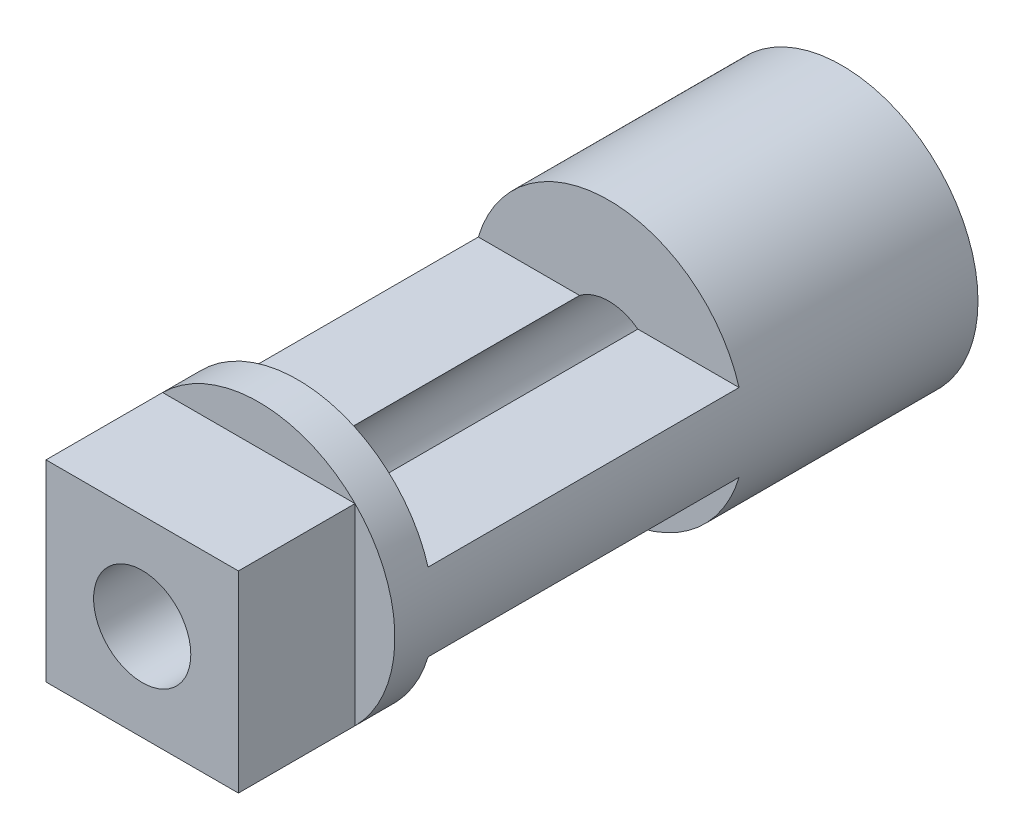
SolidWorks part; units mm, degrees
ref_plane "Front Plane" through (0, 0, 0) normal (0, 0, 1) x (1, 0, 0)
ref_plane "Top Plane" through (0, 0, 0) normal (0, 1, 0) x (1, 0, 0)
ref_plane "Right Plane" through (0, 0, 0) normal (1, 0, 0) x (0, 0, -1)
sketch "Sketch3" plane through (0, 0, 0) normal (0, 0, 1) x (1, 0, 0)
  circle A0 centre (0, 0) radius 1.25 construction
  circle A1 centre (0, 0) radius 1.25
  circle A2 centre (0, 0) radius 3.5 construction
  circle A3 centre (0, 0) radius 3.5
extrude "Boss-Extrude1" add sketch "Sketch3" along normal up to vertex (23 mm away) from vertex at 5
sketch "Sketch4" plane through (0, 0, 0) normal (1, 0, 0) x (0, 0, -1)
  line L0 (-23, 0) -> (-26, 0) construction
  line L1 (-19, 3.5) -> (-11, 3.5)
  line L2 (-19, 3.5) -> (-19, 1)
  line L3 (-19, 1) -> (-11, 1)
  line L4 (-11, 3.5) -> (-11, 1)
  line L5 (-5, 3.5) -> (-23, 3.5) construction
  dimension "D1" = 1
extrude "Cut-Extrude1" cut sketch "Sketch4" against normal through all both and the other way through all
mirror "Mirror1" about plane through (0, 0, 0) normal (0, 1, 0) of "Cut-Extrude1"
sketch "Sketch5" plane through (0, 0, 23) normal (0, 0, 1) x (1, 0, 0)
  line L1 (-2.4749, -2.4749) -> (2.4749, -2.4749)
  line L2 (-2.4749, -2.4749) -> (-2.4749, 2.4749)
  line L3 (-2.4749, 2.4749) -> (2.4749, 2.4749)
  line L4 (2.4749, -2.4749) -> (2.4749, 2.4749)
  line L5 (-2.4749, -2.4749) -> (2.4749, 2.4749) construction
  line L6 (-2.4749, 2.4749) -> (2.4749, -2.4749) construction
  circle A0 centre (0, 0) radius 3.5 construction
  point P0 (0, 0)
extrude "Cut-Extrude2" cut sketch "Sketch5" against normal blind 3 flip side to cut
